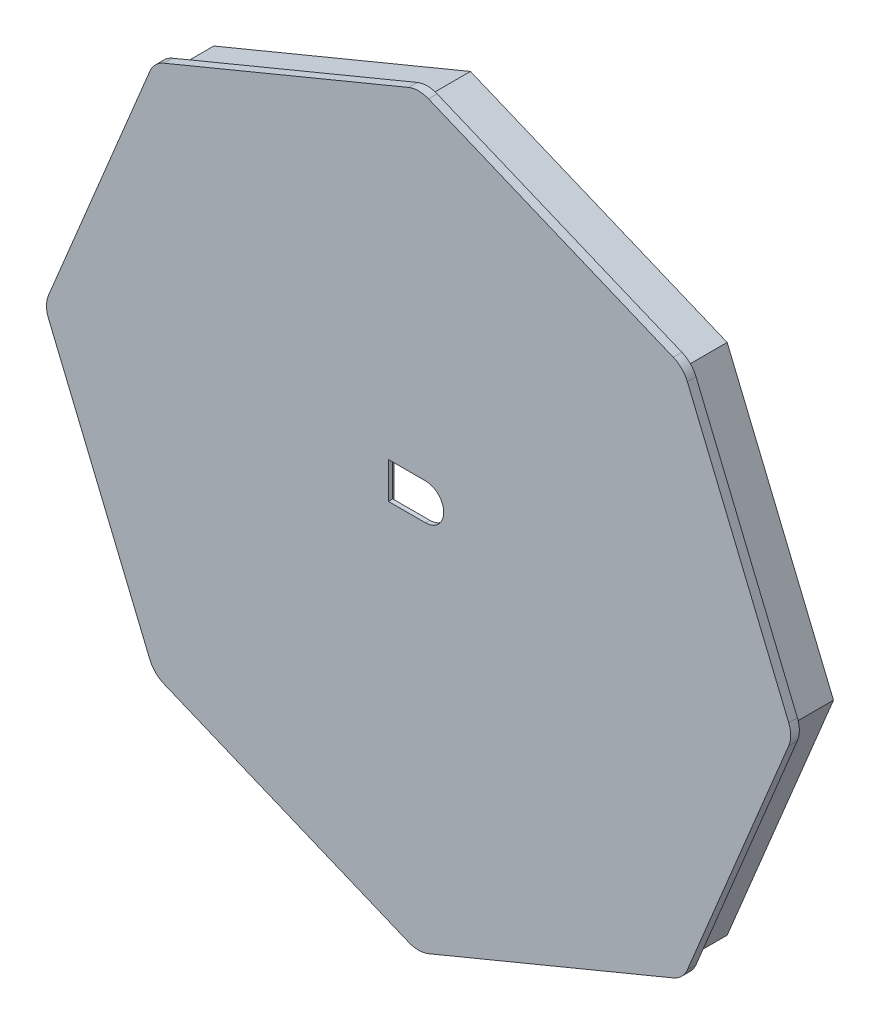
SolidWorks part; units mm, degrees
ref_plane "Plan de face" through (0, 0, 0) normal (0, 0, 1) x (1, 0, 0)
ref_plane "Plan de dessus" through (0, 0, 0) normal (0, 1, 0) x (1, 0, 0)
ref_plane "Plan de droite" through (0, 0, 0) normal (1, 0, 0) x (0, 0, -1)
sketch "Esquisse1" plane through (0, 0, 0) normal (0, 0, 1) x (1, 0, 0)
  line L29 (-19.3259, 52.1603) -> (-47.6445, 40.4304)
  line L30 (-49.2681, 38.8068) -> (-60.998, 10.4882)
  line L31 (-60.998, 8.1921) -> (-49.2681, -20.1264)
  line L32 (-47.6445, -21.75) -> (-19.3259, -33.48)
  line L33 (-17.0298, -33.48) -> (11.2888, -21.75)
  line L34 (12.9123, -20.1264) -> (24.6423, 8.1921)
  line L35 (24.6423, 10.4882) -> (12.9123, 38.8068)
  line L36 (11.2888, 40.4304) -> (-17.0298, 52.1603)
  arc A24 (-47.6445, 40.4304) -> (-49.2681, 38.8068) centre (-46.4964, 37.6588) ccw
  arc A25 (-60.998, 10.4882) -> (-60.998, 8.1921) centre (-58.2264, 9.3402) ccw
  arc A26 (-49.2681, -20.1264) -> (-47.6445, -21.75) centre (-46.4964, -18.9784) ccw
  arc A27 (-19.3259, -33.48) -> (-17.0298, -33.48) centre (-18.1779, -30.7083) ccw
  arc A28 (11.2888, -21.75) -> (12.9123, -20.1264) centre (10.1407, -18.9784) ccw
  arc A29 (24.6423, 8.1921) -> (24.6423, 10.4882) centre (21.8706, 9.3402) ccw
  arc A30 (12.9123, 38.8068) -> (11.2888, 40.4304) centre (10.1407, 37.6588) ccw
  arc A31 (-17.0298, 52.1603) -> (-19.3259, 52.1603) centre (-18.1779, 49.3887) ccw
extrude "Boss.-Extru.1" add sketch "Esquisse1" along normal blind 1
sketch "Esquisse2" plane through (0, 0, 1) normal (0, 0, 1) x (1, 0, 0)
  line L8 (-21.6717, 13.7151) -> (-17.3717, 13.7151)
  line L13 (-21.6717, 9.5151) -> (-17.3717, 9.5151)
  line L14 (-21.6717, 13.7151) -> (-21.6717, 9.5151)
  arc A9 (-17.3717, 13.7151) -> (-17.3717, 9.5151) centre (-17.3717, 11.6151) cw
extrude "Enlèv. mat.-Extru.1" cut sketch "Esquisse2" against normal blind 1
sketch "Esquisse3" plane through (0, 0, 0) normal (0, 0, -1) x (-1, 0, 0)
  line L63 (47.1087, 38.2711) -> (18.1779, 50.2546)
  line L64 (18.1779, 50.2546) -> (-10.753, 38.2711)
  line L65 (-10.753, 38.2711) -> (-22.7366, 9.3402)
  line L66 (-22.7366, 9.3402) -> (-10.753, -19.5907)
  line L67 (-10.753, -19.5907) -> (18.1779, -31.5742)
  line L68 (18.1779, -31.5742) -> (47.1087, -19.5907)
  line L69 (47.1087, -19.5907) -> (59.0923, 9.3402)
  line L70 (59.0923, 9.3402) -> (47.1087, 38.2711)
  line L71 (47.8741, 39.0364) -> (18.1779, 51.337)
  line L72 (60.1747, 9.3402) -> (47.8741, 39.0364)
  line L73 (47.8741, -20.356) -> (60.1747, 9.3402)
  line L74 (18.1779, -32.6566) -> (47.8741, -20.356)
  line L75 (-11.5184, -20.356) -> (18.1779, -32.6566)
  line L76 (-23.8189, 9.3402) -> (-11.5184, -20.356)
  line L77 (-11.5184, 39.0364) -> (-23.8189, 9.3402)
  line L78 (18.1779, 51.337) -> (-11.5184, 39.0364)
  line L79 (47.8741, 39.0364) -> (18.1779, 51.337)
  line L80 (60.1747, 9.3402) -> (47.8741, 39.0364)
  line L81 (47.8741, -20.356) -> (60.1747, 9.3402)
  line L82 (18.1779, -32.6566) -> (47.8741, -20.356)
  line L83 (-11.5184, -20.356) -> (18.1779, -32.6566)
  line L84 (-23.8189, 9.3402) -> (-11.5184, -20.356)
  line L85 (-11.5184, 39.0364) -> (-23.8189, 9.3402)
  line L86 (18.1779, 51.337) -> (-11.5184, 39.0364)
  dimension "D1" = 0.2
  dimension "D2" = 1
extrude "Boss.-Extru.2" add sketch "Esquisse3" along normal blind 5
sketch "Esquisse4" plane through (0, 0, 0) normal (0, 0, -1) x (-1, 0, 0)
  line L13 (22.0264, 7.9151) -> (22.0264, 15.3151)
  line L14 (22.0264, 15.3151) -> (13.2264, 15.3151)
  line L15 (13.2264, 15.3151) -> (13.2264, 7.9151)
  line L16 (13.2264, 7.9151) -> (22.0264, 7.9151)
  line L17 (22.0264, 7.9151) -> (22.0264, 15.3151)
  line L18 (22.0264, 15.3151) -> (13.2264, 15.3151)
  line L19 (13.2264, 15.3151) -> (13.2264, 7.9151)
  line L20 (13.2264, 7.9151) -> (22.0264, 7.9151)
  dimension "D1" = 1
extrude "Enlèv. mat.-Extru.2" cut sketch "Esquisse4" against normal blind 0.5
